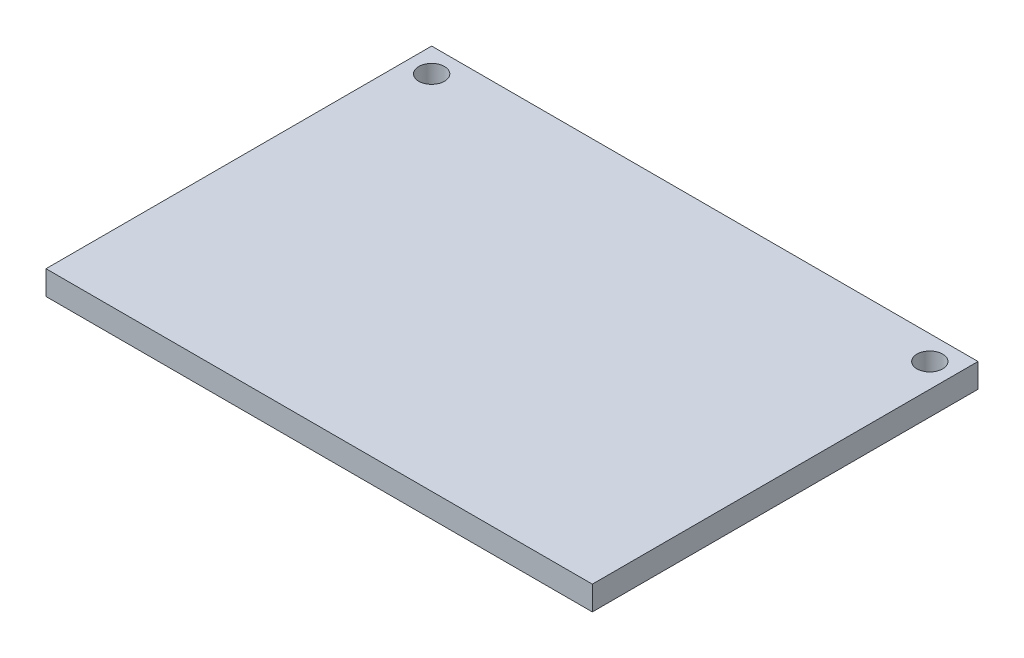
SolidWorks part; units mm, degrees
ref_plane "Front Plane" through (0, 0, 0) normal (0, 0, 1) x (1, 0, 0)
ref_plane "Top Plane" through (0, 0, 0) normal (0, 1, 0) x (1, 0, 0)
ref_plane "Right Plane" through (0, 0, 0) normal (1, 0, 0) x (0, 0, -1)
sketch "Sketch5" plane through (0, 0, 0) normal (0, 1, 0) x (1, 0, 0)
  line L1 (-43.7957, 25.4649) -> (-111.7957, 25.4649)
  line L2 (-43.7957, 25.4649) -> (-43.7957, -22.5351)
  line L3 (-43.7957, -22.5351) -> (-111.7957, -22.5351)
  line L4 (-111.7957, 25.4649) -> (-111.7957, -22.5351)
  circle A0 centre (-108.7957, 22.4649) radius 1.6
  circle A1 centre (-46.7957, 22.4649) radius 1.6
  dimension "D3" = 3
  dimension "D1" = 68
  dimension "D2" = 48
  dimension "D4" = 3
  dimension "D5" = 3
  dimension "D6" = 3
extrude "Boss-Extrude2" add sketch "Sketch5" along normal blind 3
